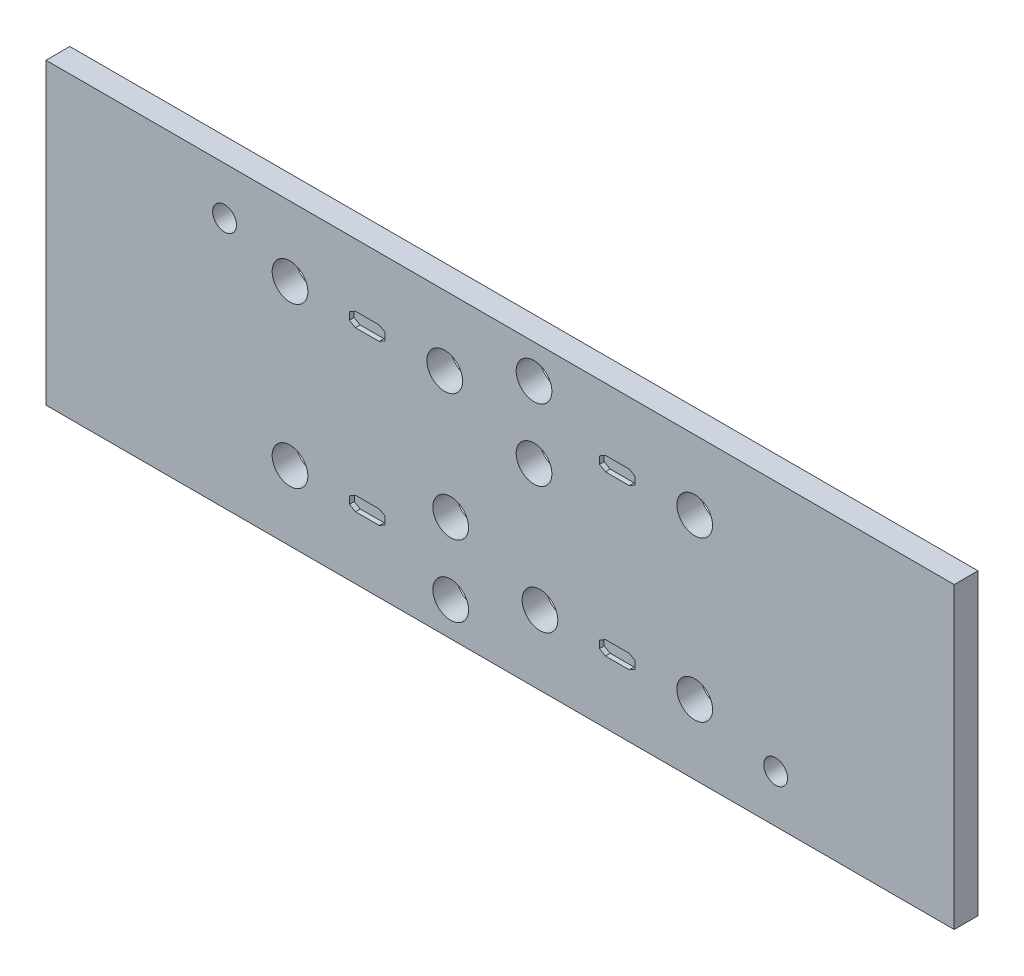
SolidWorks part; units mm, degrees
ref_plane "Front Plane" through (0, 0, 0) normal (0, 0, 1) x (1, 0, 0)
ref_plane "Top Plane" through (0, 0, 0) normal (0, 1, 0) x (1, 0, 0)
ref_plane "Right Plane" through (0, 0, 0) normal (1, 0, 0) x (0, 0, -1)
sketch "Sketch1" plane through (0, 0, 0) normal (0, 0, 1) x (1, 0, 0)
  line L0 (0, 25.1) -> (76.3, 25.1)
  line L1 (76.3, 0) -> (0, 0)
  line L2 (76.3, 25.1) -> (76.3, 0)
  line L3 (0, 25.1) -> (0, 0)
extrude "Boss-Extrude1" add sketch "Sketch1" along normal blind 2 contours L0 L2 L1 L3
sketch "Sketch3" plane through (0, 0, 2) normal (0, 0, 1) x (1, 0, 0)
  line L1 (0, 25.1) -> (76.3, 25.1) construction
  line L2 (76.3, 0) -> (0, 0) construction
  line L4 (0, 25.1) -> (0, 0) construction
  line L6 (76.3, 25.1) -> (76.3, 0) construction
  circle A2 centre (15, 21.1) radius 1
  circle A3 centre (61.3, 4) radius 1
  dimension "D1" = 2
  dimension "D2" = 2
  dimension "D3" = 15
  dimension "D4" = 4
  dimension "D5" = 15
  dimension "D6" = 4
extrude "Cut-Extrude2" cut sketch "Sketch3" against normal blind 10
sketch "Sketch10" plane through (0, 0, 2) normal (0, 0, 1) x (1, 0, 0)
  line L0 (76.3, 25.1) -> (76.3, 0) construction
  line L1 (76.3, 0) -> (0, 0) construction
  line L2 (0, 25.1) -> (76.3, 25.1) construction
  line L4 (0, 25.1) -> (0, 0) construction
  circle A1 centre (20.5, 19.2511) radius 1.5
  circle A5 centre (20.5, 5.8489) radius 1.5
  circle A10 centre (54.5, 5.8489) radius 1.5
  circle A14 centre (54.5, 19.2511) radius 1.5
  circle A15 centre (33.5, 19.2511) radius 1.5
  circle A16 centre (41.5, 5.8489) radius 1.5
  circle A17 centre (34, 2.85) radius 1.5
  circle A18 centre (34, 8.85) radius 1.5
  circle A19 centre (41, 22.25) radius 1.5
  circle A20 centre (41, 16.25) radius 1.5
  dimension "D1" = 20.5
  dimension "D2" = 21.8
  dimension "D3" = 33.5
  dimension "D4" = 3
  dimension "D5" = 3
  dimension "D6" = 34.8
  dimension "D7" = 34
  dimension "D8" = 2.85
  dimension "D9" = 3
  dimension "D10" = 3
  dimension "D11" = 3
  dimension "D12" = 3
  dimension "D14" = 3
  dimension "D17" = 3
  dimension "D13" = 8.85
  dimension "D15" = 2.85
  dimension "D16" = 35.3
  dimension "D18" = 6
extrude "Cut-Extrude8" cut sketch "Sketch10" against normal blind 2
sketch "Sketch11" plane through (0, 0, 2) normal (0, 0, 1) x (1, 0, 0)
  line L0 (37.5, 25.1) -> (37.5, -0.0753) construction
  line L4 (0, 25.1) -> (0, 0) construction
  dimension "D9" = 37.5
sketch "Sketch12" plane through (0, 0, 2) normal (0, 0, 1) x (1, 0, 0)
  line L0 (21.9868, 19.45) -> (31.9868, 19.45) construction
  line L2 (25.9868, 19.8345) -> (27.9868, 19.8345)
  line L6 (27.9868, 18.6345) -> (25.9868, 18.6345)
  line L9 (25.4868, 18.9232) -> (25.9868, 18.6345)
  line L10 (30.041, 19.05) -> (21.9865, 19.05) construction
  line L11 (0, 25.1) -> (76.3, 25.1) construction
  line L12 (25.4868, 19.5458) -> (25.4868, 18.9232)
  line L13 (25.4868, 19.5458) -> (25.9868, 19.8345)
  line L14 (27.9868, 19.8345) -> (28.4868, 19.5458)
  line L15 (28.4868, 19.5458) -> (28.4868, 18.9232)
  line L16 (28.4868, 18.9232) -> (27.9868, 18.6345)
  line L17 (43, 5.8489) -> (53, 5.8489) construction
  line L18 (49.5, 6.1589) -> (49.5, 5.5369)
  line L19 (49.5, 5.5369) -> (48.9994, 5.2479)
  line L20 (48.9994, 5.2479) -> (46.9994, 5.2479)
  line L21 (46.9994, 5.2479) -> (46.5, 5.5376)
  line L22 (46.5, 5.5376) -> (46.5, 6.1596)
  line L23 (46.5, 6.1596) -> (46.9994, 6.4479)
  line L24 (46.9994, 6.4479) -> (48.9994, 6.4479)
  line L25 (48.9994, 6.4479) -> (49.5, 6.1589)
  line L26 (22, 5.8489) -> (30.041, 5.8489) construction
  line L27 (25.5, 6.1596) -> (25.5, 5.5376)
  line L28 (25.5, 5.5376) -> (26.0006, 5.2486)
  line L29 (26.0006, 5.2486) -> (28.0006, 5.2486)
  line L33 (28.0006, 6.4486) -> (26.0006, 6.4486)
  line L34 (26.0006, 6.4486) -> (25.5, 6.1596)
  line L35 (28.0006, 6.4486) -> (28.5, 6.1602)
  line L36 (28.5, 6.1602) -> (28.5, 5.5376)
  line L37 (28.5, 5.5376) -> (28.0006, 5.2486)
  line L38 (53, 19.2511) -> (44, 19.2511) construction
  line L39 (49.5, 19.5631) -> (49.5, 18.9411)
  line L40 (49.5, 18.9411) -> (48.9994, 18.6521)
  line L41 (48.9994, 18.6521) -> (46.9994, 18.6521)
  line L42 (46.9994, 18.6521) -> (46.4989, 18.9411)
  line L43 (46.4989, 18.9411) -> (46.4989, 19.5631)
  line L44 (46.4989, 19.5631) -> (46.9994, 19.8521)
  line L45 (46.9994, 19.8521) -> (48.9994, 19.8521)
  line L46 (48.9994, 19.8521) -> (49.5, 19.5631)
  circle A0 centre (20.5, 19.2511) radius 1.5 construction
  circle A1 centre (20.5, 5.8489) radius 1.5 construction
  circle A2 centre (54.5, 19.2511) radius 1.5 construction
  circle A3 centre (41.5, 5.8489) radius 1.5 construction
  circle A4 centre (54.5, 5.8489) radius 1.5 construction
  point P18 (26.9868, 19.45)
  point P38 (25.5, 5.8486)
  dimension "D1" = 3.5003
  dimension "D2" = 10
  dimension "D3" = 5.65
  dimension "D4" = 1.2
  dimension "D5" = 3.5
  dimension "D6" = 120
  dimension "D7" = 120
  dimension "D8" = 2
  dimension "D9" = 3
  dimension "D10" = 3.5
  dimension "D11" = 0.31
  dimension "D12" = 0.622
  dimension "D13" = 0.622
  dimension "D14" = 3
  dimension "D15" = 2
  dimension "D16" = 1.2
  dimension "D17" = 120
  dimension "D18" = 120
  dimension "D19" = 120
  dimension "D20" = 3.5
  dimension "D21" = 0.622
  dimension "D22" = 0.3106
  dimension "D23" = 120
  dimension "D24" = 120
  dimension "D25" = 2
  dimension "D26" = 1.2
  dimension "D27" = 3
  dimension "D28" = 0.622
  dimension "D29" = 0.31
  dimension "D30" = 3.5
  dimension "D31" = 9
  dimension "D32" = 120
  dimension "D33" = 120
  dimension "D34" = 2
  dimension "D35" = 1.2
  dimension "D36" = 120
  dimension "D37" = 0.622
extrude "Cut-Extrude10" cut sketch "Sketch12" against normal blind 0.4
